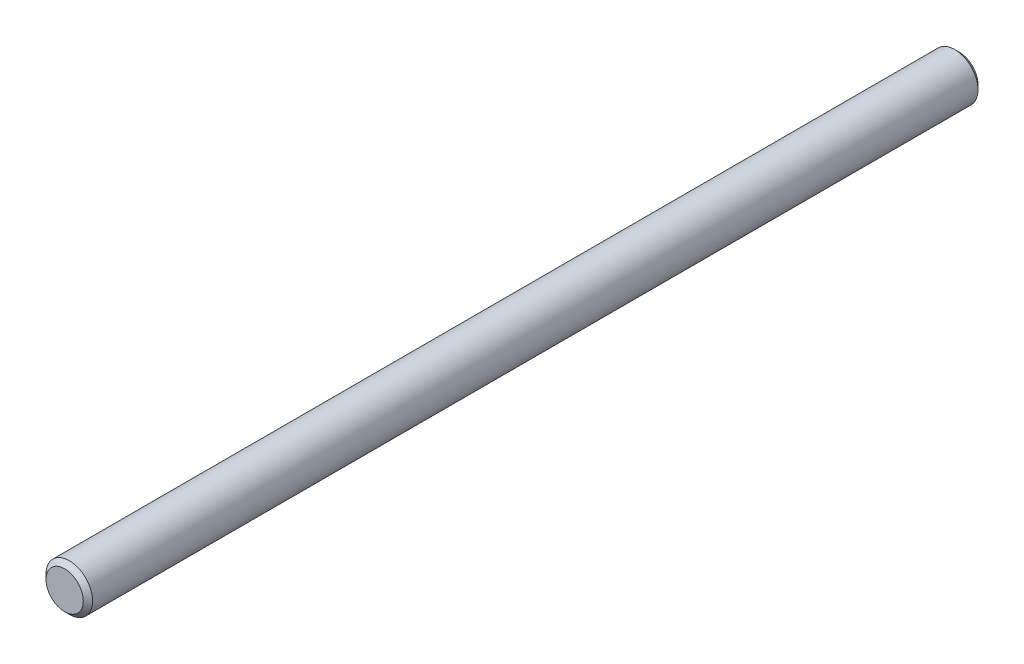
SolidWorks part; units mm, degrees
ref_plane "Front Plane" through (0, 0, 0) normal (0, 0, 1) x (1, 0, 0)
ref_plane "Top Plane" through (0, 0, 0) normal (0, 1, 0) x (1, 0, 0)
ref_plane "Right Plane" through (0, 0, 0) normal (1, 0, 0) x (0, 0, -1)
sketch "Sketch1" plane through (0, 0, 0) normal (0, 0, 1) x (1, 0, 0)
  line L0 (-3.9688, 0) -> (3.9688, 0) construction
  circle A0 centre (0, 0) radius 3.9688
  point P3 (-3.9688, 0)
  point P4 (3.9688, 0)
  dimension "OD" = 7.9375
extrude "Extrude1" add sketch "Sketch1" along normal mid plane 152.4
chamfer "Chamfer1" distance 0.7937 angle 45 2 edges at (3.9688, 0, -76.2) (3.9688, 0, 76.2)
equation "\"D1@Chamfer1\" = \"OD@Sketch1\"*.1"
